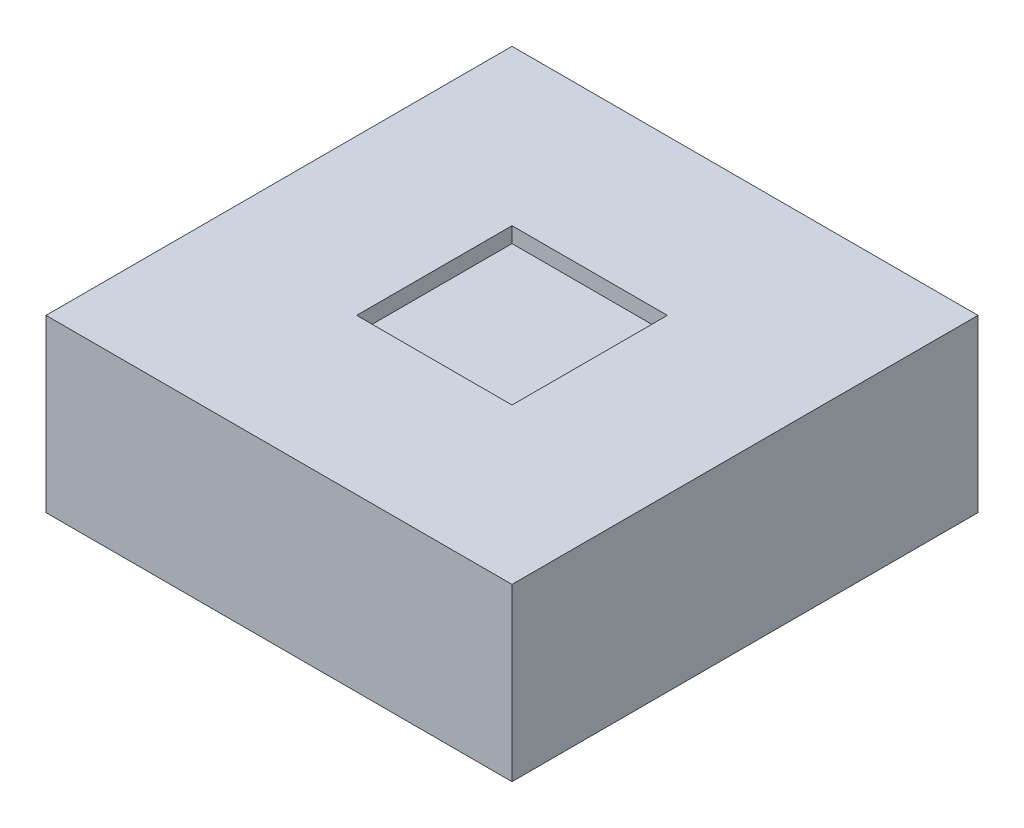
SolidWorks part; units mm, degrees
ref_plane "Front Plane" through (0, 0, 0) normal (0, 0, 1) x (1, 0, 0)
ref_plane "Top Plane" through (0, 0, 0) normal (0, 1, 0) x (1, 0, 0)
ref_plane "Right Plane" through (0, 0, 0) normal (1, 0, 0) x (0, 0, -1)
sketch "Sketch1" plane through (0, 0, 0) normal (0, 1, 0) x (1, 0, 0)
  line L1 (-15, -15) -> (15, -15)
  line L2 (-15, -15) -> (-15, 15)
  line L3 (-15, 15) -> (15, 15)
  line L4 (15, -15) -> (15, 15)
  line L5 (-15, -15) -> (15, 15) construction
  line L6 (-15, 15) -> (15, -15) construction
  point P0 (0, 0)
extrude "Boss-Extrude1" add sketch "Sketch1" along normal blind 10
sketch "Sketch2" plane through (0, 10, 0) normal (0, 1, 0) x (1, 0, 0)
  line L1 (-15, -15) -> (15, -15)
  line L2 (-15, -15) -> (-15, 15)
  line L3 (-15, 15) -> (15, 15)
  line L4 (15, -15) -> (15, 15)
  line L5 (-15, -15) -> (15, 15) construction
  line L6 (-15, 15) -> (15, -15) construction
  line L11 (-5, -5) -> (5, -5)
  line L12 (-5, -5) -> (-5, 5)
  line L13 (-5, 5) -> (5, 5)
  line L14 (5, -5) -> (5, 5)
  line L15 (-5, -5) -> (5, 5) construction
  line L16 (-5, 5) -> (5, -5) construction
  point P0 (0, 0)
  point P7 (0, 0)
extrude "Boss-Extrude2" add sketch "Sketch2" along normal blind 1
